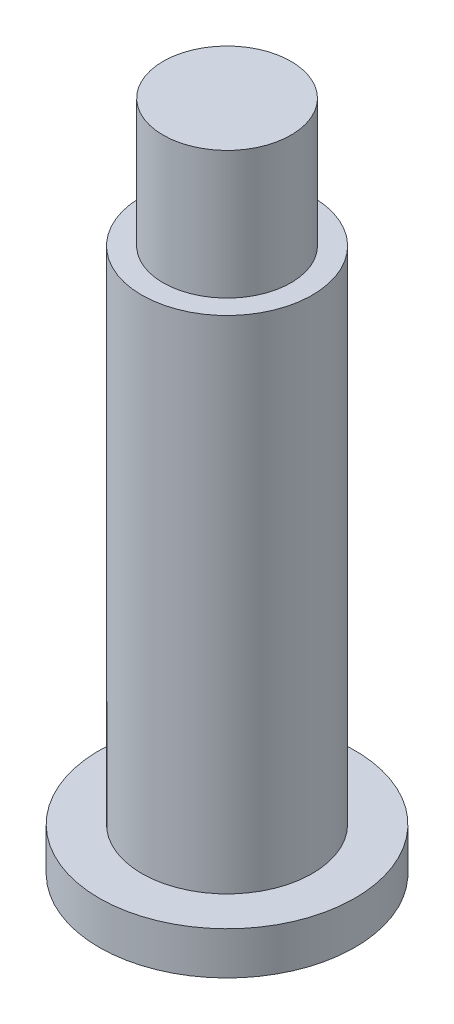
SolidWorks part; units mm, degrees
ref_plane "前视基准面" through (0, 0, 0) normal (0, 0, 1) x (1, 0, 0)
ref_plane "上视基准面" through (0, 0, 0) normal (0, 1, 0) x (1, 0, 0)
ref_plane "右视基准面" through (0, 0, 0) normal (1, 0, 0) x (0, 0, -1)
sketch "草图1" plane through (0, 0, 0) normal (0, 1, 0) x (1, 0, 0)
  circle A0 centre (0, 0) radius 6
  dimension "D1" = 12
extrude "凸台-拉伸1" add sketch "草图1" along normal blind 2
sketch "草图2" plane through (0, 2, 0) normal (0, 1, 0) x (1, 0, 0)
  circle A0 centre (0, 0) radius 4
  dimension "D1" = 8
extrude "凸台-拉伸2" add sketch "草图2" along normal blind 23.5
sketch "草图3" plane through (0, 25.5, 0) normal (0, 1, 0) x (1, 0, 0)
  circle A0 centre (0, 0) radius 3
  dimension "D1" = 6
extrude "凸台-拉伸3" add sketch "草图3" along normal blind 6
cosmetic thread "装饰螺纹线1" parameters "D1"=6, "D2"=5
